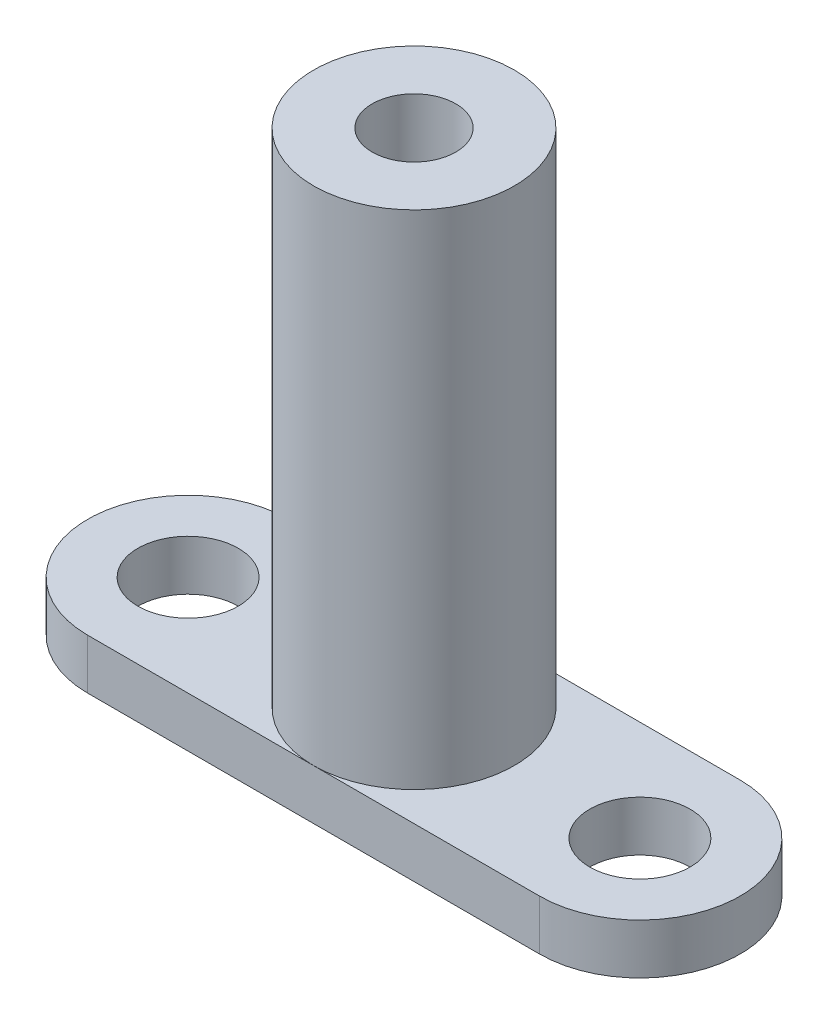
SolidWorks part; units mm, degrees
ref_plane "前视基准面" through (0, 0, 0) normal (0, 0, 1) x (1, 0, 0)
ref_plane "上视基准面" through (0, 0, 0) normal (0, 1, 0) x (1, 0, 0)
ref_plane "右视基准面" through (0, 0, 0) normal (1, 0, 0) x (0, 0, -1)
sketch "草图1" plane through (0, 0, 0) normal (0, 1, 0) x (1, 0, 0)
  line L0 (-13.5, 6) -> (13.5, 6)
  line L1 (-13.5, -6) -> (13.5, -6)
  circle A0 centre (-13.5, 0) radius 6
  circle A1 centre (13.5, 0) radius 6
  dimension "D1" = 12
  dimension "D2" = 13.5
  dimension "D3" = 13.5
extrude "凸台-拉伸1" add sketch "草图1" along normal blind 3 contours A0 | A1 L0 A0 L1 | A1
sketch "草图2" plane through (0, 3, 0) normal (0, 1, 0) x (1, 0, 0)
  circle A0 centre (0, 0) radius 6
extrude "凸台-拉伸2" add sketch "草图2" along normal blind 30
hole_wizard "M6 螺纹孔1" positions "草图3" profile "草图5" tap size "M6" standard "GB" end condition through all
sketch "草图3" plane through (0, 33, 0) normal (0, 1, 0) x (1, 0, 0)
  point P0 (0, 0)
sketch "草图5" plane through (0, 33, 0) normal (1, 0, 0) x (0, 0, 1)
  line L0 (0, 0) -> (0, 33)
  line L1 (0, 33) -> (2.5, 33)
  line L2 (2.5, 33) -> (2.5, 0)
  line L5 (2.5, 0) -> (0, 0)
  line L11 (0, -6.35) -> (0, 107.95) construction
  dimension "通孔螺纹孔钻头直径" = 5
  dimension "通孔螺纹孔钻头深度" = 33
cosmetic thread "孔螺蚊线1" parameters "D2"=6
sketch "草图6" plane through (0, 3, 0) normal (0, 1, 0) x (1, 0, 0)
  circle A0 centre (-13.5, 0) radius 3
  circle A1 centre (13.5, 0) radius 3
  dimension "D1" = 6
  dimension "D2" = 6
extrude "切除-拉伸1" cut sketch "草图6" against normal blind 10
